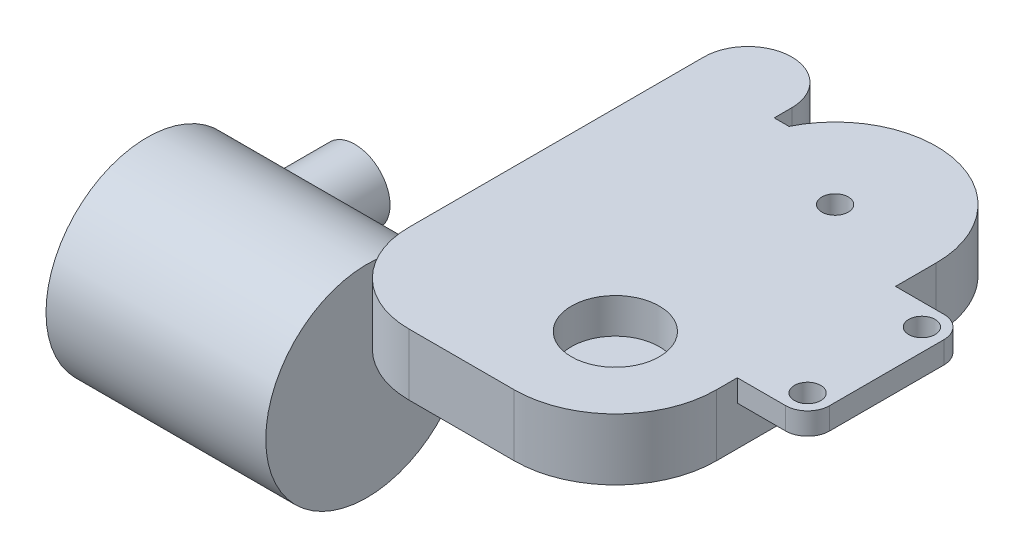
SolidWorks part; units mm, degrees
material "ABS"
ref_plane "Front Plane" through (0, 0, 0) normal (0, 0, 1) x (1, 0, 0)
ref_plane "Top Plane" through (0, 0, 0) normal (0, 1, 0) x (1, 0, 0)
ref_plane "Right Plane" through (0, 0, 0) normal (1, 0, 0) x (0, 0, -1)
sketch "Sketch1" plane through (0, 0, 0) normal (0, 1, 0) x (1, 0, 0)
  line L0 (0, -26.0333) -> (0, 26.0333) construction
  line L5 (28.5, 13.6281) -> (28.5, -11.3719)
  line L6 (5, 20.7013) -> (5, 18.7013)
  line L8 (17, -22.8719) -> (5, -22.8719)
  line L9 (-5, 20.7013) -> (-5, -12.8719)
  line L10 (5, 18.7013) -> (6.6795, 18.7013)
  arc A4 (17, -22.8719) -> (28.5, -11.3719) centre (17, -11.3719) ccw
  circle A5 centre (17, 13.6281) radius 1.5 construction
  arc A8 (5, 20.7013) -> (-5, 20.7013) centre (0, 20.7013) ccw
  arc A9 (28.5, 13.6281) -> (6.6795, 18.7013) centre (17, 13.6281) ccw
  arc A10 (-5, -12.8719) -> (5, -22.8719) centre (5, -12.8719) ccw
  point P0 (0, 0)
  dimension "D4" = 23
  dimension "D5" = 3
  dimension "D6" = 36.3
  dimension "D7" = 17
  dimension "D8" = 11.5
  dimension "D9" = 10
  dimension "D10" = 0
  dimension "D2" = 7
  dimension "D11" = 10
  dimension "D1" = 25
extrude "Boss-Extrude1" add sketch "Sketch1" along normal blind 7 contours A4 L5 A9 L10 L6 A8 L9 A10 L8
sketch "Sketch2" plane through (0, 0, 0) normal (0, -1, 0) x (1, 0, 0)
  circle A0 centre (0, -20.7013) radius 2.5
  dimension "D1" = 5
extrude "Cut-Extrude1" cut sketch "Sketch2" against normal blind 4
sketch "Sketch3" plane through (0, 7, 0) normal (0, 1, 0) x (1, 0, 0)
  circle A0 centre (17, 13.6281) radius 1.5
  circle A1 centre (17, -11.3719) radius 5
  dimension "D1" = 3
  dimension "D2" = 10
extrude "Cut-Extrude2" cut sketch "Sketch3" against normal blind 4
sketch "Sketch4" plane through (-5, 0, 0) normal (-1, 0, 0) x (0, 0, 1)
  line L0 (-20.7013, 7) -> (12.8719, 7) construction
  circle A0 centre (17.6378, -5.75) radius 11.5
  dimension "D1" = 23
  dimension "D2" = 12.75
extrude "Boss-Extrude2" add sketch "Sketch4" along normal blind 25
ref_plane "Plane2" through (0, 0, 10) normal (0, 0, 1) x (1, 0, 0)
sketch "Sketch5" plane through (0, 0, 10) normal (0, 0, 1) x (1, 0, 0)
  line L0 (26.0333, 0) -> (-26.0333, 0) construction
  line L1 (0, -14.025) -> (0, 14.025) construction
  circle A0 centre (-25, -5.75) radius 4
  dimension "D1" = 8
  dimension "D2" = 5.75
  dimension "D3" = 25
extrude "Boss-Extrude3" add sketch "Sketch5" against normal blind 11
sketch "Sketch6" plane through (0, 7, 0) normal (0, 1, 0) x (1, 0, 0)
  line L0 (-3.85, 0) -> (3.85, 0) construction
  line L5 (28.5, 9) -> (34, 9)
  line L6 (28.5, 9) -> (28.5, -9)
  line L7 (28.5, -9) -> (34, -9)
  line L8 (36.5, 6.5) -> (36.5, -6.5)
  line L9 (28.5, 9) -> (36.5, -9) construction
  line L10 (28.5, -9) -> (36.5, 9) construction
  line L11 (28.5, 13.6281) -> (28.5, -11.3719) construction
  circle A0 centre (34, -6.5) radius 1.5
  circle A1 centre (34, 6.5) radius 1.5
  arc A2 (36.5, -6.5) -> (34, -9) centre (34, -6.5) cw
  arc A3 (36.5, 6.5) -> (34, 9) centre (34, 6.5) ccw
  point P0 (32.5, 0)
  point P12 (17, -11.3719)
  dimension "D2" = 3
  dimension "D5" = 3
  dimension "D9" = 2.5
  dimension "D1" = 0
  dimension "D3" = 17
  dimension "D4" = 6.5
  dimension "D6" = 6.5
  dimension "D7" = 1
  dimension "D8" = 1
extrude "Boss-Extrude4" add sketch "Sketch6" against normal blind 2.5
sketch "Sketch8" plane through (0, 7, 0) normal (0, 1, 0) x (1, 0, 0)
  line L0 (36.5, -6.5) -> (36.5, 6.5) construction
  line L2 (-13.3375, 0) -> (13.3375, 0) construction
  circle A0 centre (34, 6.5) radius 1.5 construction
  circle A2 centre (34, -6.5) radius 1.5 construction
  point P0 (57, 8.5)
  point P5 (34, 29.5)
  point P8 (34, -29.5)
  point P12 (57, -8.5)
  dimension "D1" = 20.5
  dimension "D2" = 8.5
  dimension "D3" = 0
  dimension "D4" = 23
  dimension "D5" = 0
  dimension "D6" = 23
  dimension "D7" = 8.5
ref_plane "Plane3" through (30.1469, 0, -33.018) normal (0.6743, 0, -0.7385) x (-0.7385, 0, -0.6743)
ref_plane "Plane4" through (30.1469, 0, 33.018) normal (-0.6743, 0, -0.7385) x (-0.7385, 0, 0.6743)
equation "\"D5@Sketch6\"=\"D2@Sketch6\""
equation "\"D6@Sketch6\"=\"D4@Sketch6\""
